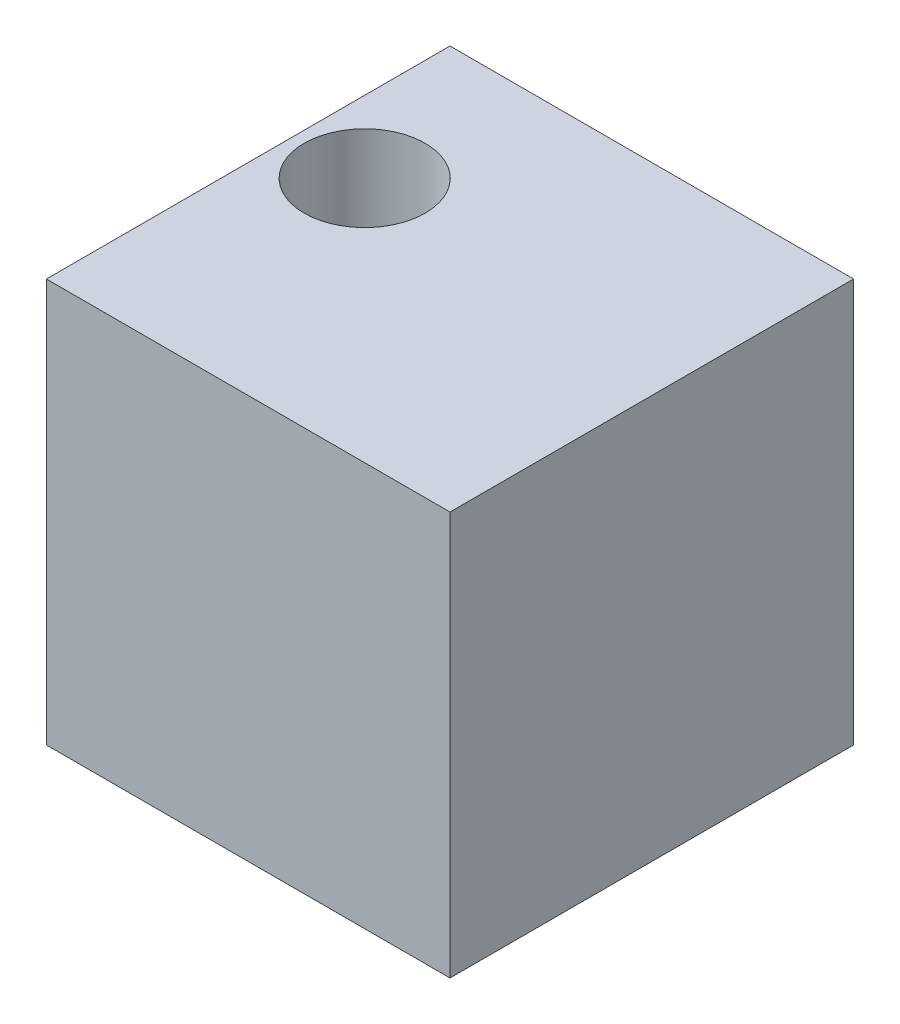
SolidWorks part; units mm, degrees
ref_plane "Front Plane" through (0, 0, 0) normal (0, 0, 1) x (1, 0, 0)
ref_plane "Top Plane" through (0, 0, 0) normal (0, 1, 0) x (1, 0, 0)
ref_plane "Right Plane" through (0, 0, 0) normal (1, 0, 0) x (0, 0, -1)
sketch "Sketch1" plane through (0, 0, 0) normal (0, 0, 1) x (1, 0, 0)
  line L1 (0, 0) -> (25.4, 0)
  line L2 (0, 0) -> (0, 25.4)
  line L3 (0, 25.4) -> (25.4, 25.4)
  line L4 (25.4, 0) -> (25.4, 25.4)
  dimension "D1" = 25.4
  dimension "D2" = 25.4
extrude "Boss-Extrude1" add sketch "Sketch1" along normal blind 25.4
sketch "Sketch3" plane through (0, 25.4, 0) normal (0, 1, 0) x (1, 0, 0)
  circle A0 centre (4.5205, -9.8911) radius 3.81
  dimension "D1" = 7.62
extrude "Cut-Extrude1" cut sketch "Sketch3" against normal through all contours A0
